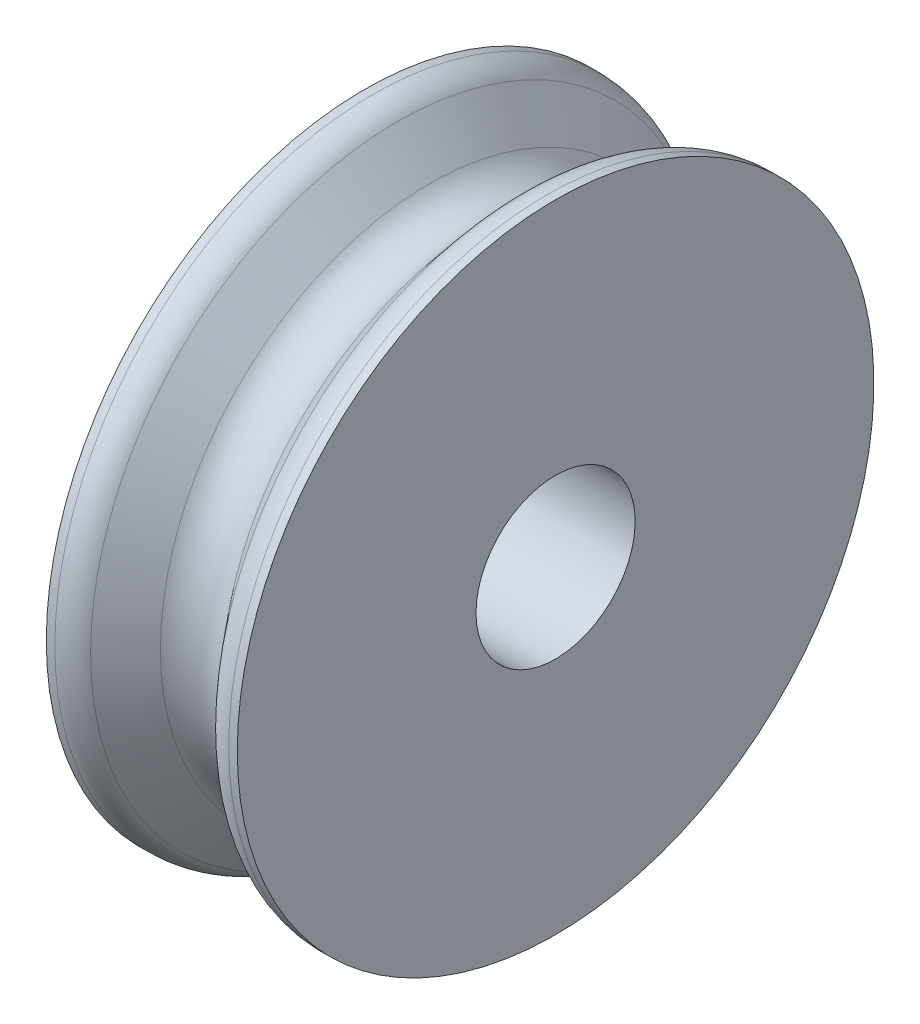
SolidWorks part; units mm, degrees
ref_plane "Front Plane" through (0, 0, 0) normal (0, 0, 1) x (1, 0, 0)
ref_plane "Top Plane" through (0, 0, 0) normal (0, 1, 0) x (1, 0, 0)
ref_plane "Right Plane" through (0, 0, 0) normal (1, 0, 0) x (0, 0, -1)
sketch "Sketch1" plane through (0, 0, 0) normal (0, 0, 1) x (1, 0, 0)
  line L1 (-11.3287, 50) -> (-15, 50)
  line L2 (-15, 50) -> (-15, 12.5)
  line L5 (-15, 12.5) -> (0, 12.5)
  line L6 (0, 12.5) -> (0, 40)
  line L10 (-11.3287, 50) -> (-4.8261, 42.2504)
  line L11 (-75.8883, 0) -> (71.8055, 0) construction
  arc A0 (-4.8261, 42.2504) -> (0, 40) centre (0, 46.3) ccw
  dimension "D3" = 6.3
  dimension "D1" = 40
  dimension "D2" = 15
  dimension "D4" = 50
  dimension "D5" = 40
  dimension "D6" = 12.5
revolve "Revolve1" add sketch "Sketch1" angle 360 about L11
mirror "Mirror1" about plane through (0, 12.5, 0) normal (-1, 0, 0) of "Revolve1"
fillet "Fillet1" radius 5 2 edges at (11.3287, 0, 50) (-11.3287, 0, 50)
ref_plane "Plane1" through (0, 40, 0) normal (0, 1, 0) x (1, 0, 0)
ref_plane "Plane2" through (0, 0, 0) normal (1, 0, 0) x (0, 0, -1)
sketch "Sketch2" plane through (0, 0, 0) normal (1, 0, 0) x (0, 0, -1)
  circle A0 centre (0, 0) radius 40 construction
